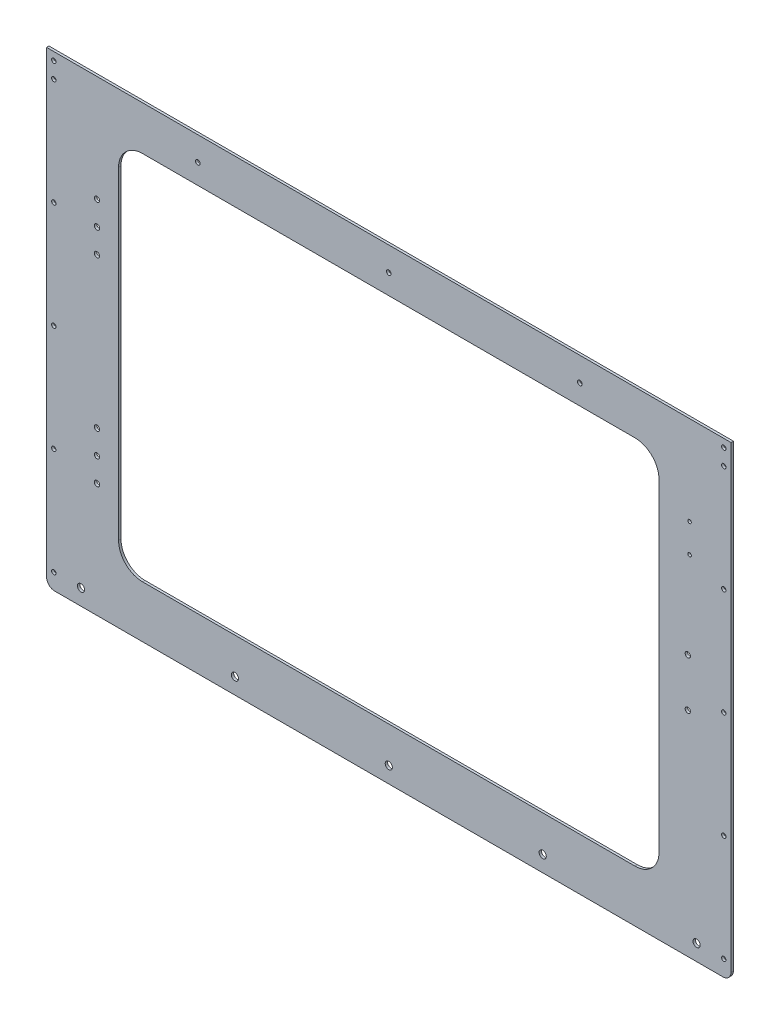
SolidWorks part; units mm, degrees
material "AISI 304"
ref_plane "Front Plane" through (0, 0, 0) normal (0, 0, 1) x (1, 0, 0)
ref_plane "Top Plane" through (0, 0, 0) normal (0, 1, 0) x (1, 0, 0)
ref_plane "Right Plane" through (0, 0, 0) normal (1, 0, 0) x (0, 0, -1)
sketch "Sketch1" plane through (0, 0, 0) normal (0, 0, 1) x (1, 0, 0)
  line L1 (0, 0) -> (856, 0)
  line L2 (0, 0) -> (0, 543.9)
  line L3 (0, 543.9) -> (856, 543.9)
  line L4 (856, 0) -> (856, 543.9)
  dimension "D1" = 856
  dimension "D2" = 543.9
extrude "MainFront" add sketch "Sketch1" along normal blind 3
sketch "Sketch2" plane through (0, 0, 3) normal (0, 0, 1) x (1, 0, 0)
  line L0 (428, 256.95) -> (428, 543.9) construction
  line L1 (90, 25) -> (766, 25)
  line L2 (90, 25) -> (90, 488.9)
  line L3 (90, 488.9) -> (766, 488.9)
  line L4 (766, 25) -> (766, 488.9)
  line L5 (90, 25) -> (766, 488.9) construction
  line L6 (90, 488.9) -> (766, 25) construction
  line L7 (856, 543.9) -> (0, 543.9) construction
  line L8 (856, 0) -> (856, 543.9) construction
  line L9 (0, 0) -> (856, 0) construction
  point P0 (428, 256.95)
  dimension "D1" = 55
  dimension "D2" = 90
  dimension "D3" = 25
extrude "DoorCut" cut sketch "Sketch2" against normal through all
fillet "DoorRoundInternal" radius 30 4 edges at (766, 25, 1.5) (90, 25, 1.5) (766, 488.9, 1.5) (90, 488.9, 1.5)
ref_plane "VerDoor" through (428, 0, 0) normal (1, 0, 0) x (0, 0, -1)
ref_plane "HorDoor" through (0, 256.95, 0) normal (0, 1, 0) x (1, 0, 0)
sketch "Sketch3" plane through (0, 0, 3) normal (0, 0, 1) x (1, 0, 0)
  line L0 (856, 0) -> (856, 543.9) construction
  line L1 (0, 0) -> (856, 0)
  line L2 (0, 0) -> (0, -40)
  line L3 (0, -40) -> (856, -40)
  line L4 (856, 0) -> (856, -40)
  dimension "D1" = 40
extrude "BottomMount" add sketch "Sketch3" against normal blind 3
hole_wizard "M8 Clearance Hole1" positions "Sketch4" profile "Sketch5" hole size "M8" standard "ISO" end condition through all
sketch "Sketch4" plane through (0, 0, 3) normal (0, 0, 1) x (1, 0, 0)
  line L0 (0, -40) -> (856, -40) construction
  line L2 (0, 543.9) -> (0, -40) construction
  point P0 (43, -20)
  dimension "D1" = 20
  dimension "D2" = 43
sketch "Sketch5" plane through (43, -20, 3) normal (1, 0, 0) x (0, -1, 0)
  line L0 (0, 0) -> (0, 3)
  line L1 (0, 3) -> (4.5, 3)
  line L2 (4.5, 3) -> (4.5, 0)
  line L5 (4.5, 0) -> (0, 0)
  line L11 (0, -6.35) -> (0, 107.95) construction
  dimension "Thru Hole Dia." = 9
  dimension "Thru Hole Depth" = 3
pattern_linear "LPattern1" count 5 spacing 192.5 along (1, 0, 0) of "M8 Clearance Hole1"
hole_wizard "M5 Clearance Hole1" positions "Sketch6" profile "Sketch8" hole size "M5" standard "ISO" end condition through all
sketch "Sketch6" plane through (0, 0, 3) normal (0, 0, 1) x (1, 0, 0)
  line L0 (0, 543.9) -> (0, -40) construction
  line L1 (0, -40) -> (856, -40) construction
  point P0 (9, -20)
  dimension "D1" = 9
  dimension "D2" = 20
sketch "Sketch8" plane through (9, -20, 3) normal (1, 0, 0) x (0, -1, 0)
  line L0 (0, 0) -> (0, 3)
  line L1 (0, 3) -> (2.75, 3)
  line L2 (2.75, 3) -> (2.75, 0)
  line L5 (2.75, 0) -> (0, 0)
  line L11 (0, -6.35) -> (0, 107.95) construction
  dimension "Thru Hole Dia." = 5.5
  dimension "Thru Hole Depth" = 3
pattern_linear "LPattern2" count 5 spacing 133.475 along (0, 1, 0) of "M5 Clearance Hole1"
mirror "Mirror1" about plane through (428, 0, 0) normal (1, 0, 0) of "LPattern2", "M5 Clearance Hole1"
hole_wizard "M5 Clearance Hole2" positions "Sketch9" profile "Sketch10" hole size "M5" standard "ISO" end condition through all
sketch "Sketch9" plane through (0, 0, 3) normal (0, 0, 1) x (1, 0, 0)
  line L0 (856, 543.9) -> (0, 543.9) construction
  line L1 (0, 543.9) -> (0, -40) construction
  point P0 (9, 533.9)
  dimension "D1" = 10
  dimension "D2" = 9
sketch "Sketch10" plane through (9, 533.9, 3) normal (1, 0, 0) x (0, -1, 0)
  line L0 (0, 0) -> (0, 3)
  line L1 (0, 3) -> (2.75, 3)
  line L2 (2.75, 3) -> (2.75, 0)
  line L5 (2.75, 0) -> (0, 0)
  line L11 (0, -6.35) -> (0, 107.95) construction
  dimension "Thru Hole Dia." = 5.5
  dimension "Thru Hole Depth" = 3
pattern_linear "LPattern3" count 2 spacing 838 along (1, 0, 0) of "M5 Clearance Hole2"
hole_wizard "M6 Clearance Hole1" positions "Sketch11" profile "Sketch12" hole size "M6" standard "ISO" end condition through all
sketch "Sketch11" plane through (0, 0, 3) normal (0, 0, 1) x (1, 0, 0)
  arc A0 (798.8, 286.95) -> (805.2, 286.95) centre (802, 286.95) ccw construction
  arc A1 (805.2, 226.95) -> (798.8, 226.95) centre (802, 226.95) ccw construction
  point P0 (802, 286.95)
  point P2 (802, 226.95)
sketch "Sketch12" plane through (802, 286.95, 3) normal (1, 0, 0) x (0, -1, 0)
  line L0 (0, 0) -> (0, 3)
  line L1 (0, 3) -> (3.3, 3)
  line L2 (3.3, 3) -> (3.3, 0)
  line L5 (3.3, 0) -> (0, 0)
  line L11 (0, -6.35) -> (0, 107.95) construction
  dimension "Thru Hole Dia." = 6.6
  dimension "Thru Hole Depth" = 3
fillet "Fillet1" radius 10 2 edges at (856, -40, 1.5) (0, -40, 1.5)
hole_wizard "M4 Clearance Hole1" positions "Sketch13" profile "Sketch14" hole size "M4" standard "ISO" end condition through all
sketch "Sketch13" plane through (0, 0, 3) normal (0, 0, 1) x (1, 0, 0)
  point P0 (804.1806, 432.409)
  point P3 (804.1806, 396.409)
sketch "Sketch14" plane through (804.1806, 432.409, 3) normal (1, 0, 0) x (0, -1, 0)
  line L0 (0, 0) -> (0, 3)
  line L1 (0, 3) -> (2.25, 3)
  line L2 (2.25, 3) -> (2.25, 0)
  line L5 (2.25, 0) -> (0, 0)
  line L11 (0, -6.35) -> (0, 107.95) construction
  dimension "Thru Hole Dia." = 4.5
  dimension "Thru Hole Depth" = 3
hole_wizard "M6 Clearance Hole2" positions "Sketch15" profile "Sketch16" hole size "M6" standard "ISO" end condition through all
sketch "Sketch15" plane through (0, 0, 3) normal (0, 0, 1) x (1, 0, 0)
  point P0 (63, 410.9)
  point P3 (63, 380.9)
  point P6 (63, 350.9)
sketch "Sketch16" plane through (63, 410.9, 3) normal (1, 0, 0) x (0, -1, 0)
  line L0 (0, 0) -> (0, 3)
  line L1 (0, 3) -> (3.3, 3)
  line L2 (3.3, 3) -> (3.3, 0)
  line L5 (3.3, 0) -> (0, 0)
  line L11 (0, -6.35) -> (0, 107.95) construction
  dimension "Thru Hole Dia." = 6.6
  dimension "Thru Hole Depth" = 3
ref_plane "Plane1" through (0, 256.95, 0) normal (0, 1, 0) x (1, 0, 0)
mirror "Mirror2" about plane through (0, 256.95, 0) normal (0, 1, 0) of "M6 Clearance Hole2"
hole_wizard "M5 Clearance Hole3" positions "Sketch17" profile "Sketch18" hole size "M5" standard "ISO" end condition through all
sketch "Sketch17" plane through (0, 0, 3) normal (0, 0, 1) x (1, 0, 0)
  line L0 (9, 513.9) -> (189, 513.9) construction
  line L1 (189, 513.9) -> (428, 513.9) construction
  line L2 (428, 513.9) -> (667, 513.9) construction
  line L3 (667, 513.9) -> (847, 513.9) construction
  point P0 (189, 513.9)
  point P2 (428, 513.9)
  point P4 (667, 513.9)
  dimension "D1" = 180
sketch "Sketch18" plane through (189, 513.9, 3) normal (1, 0, 0) x (0, -1, 0)
  line L0 (0, 0) -> (0, 3)
  line L1 (0, 3) -> (2.9, 3)
  line L2 (2.9, 3) -> (2.9, 0)
  line L5 (2.9, 0) -> (0, 0)
  line L11 (0, -6.35) -> (0, 107.95) construction
  dimension "Thru Hole Dia." = 5.8
  dimension "Thru Hole Depth" = 3
